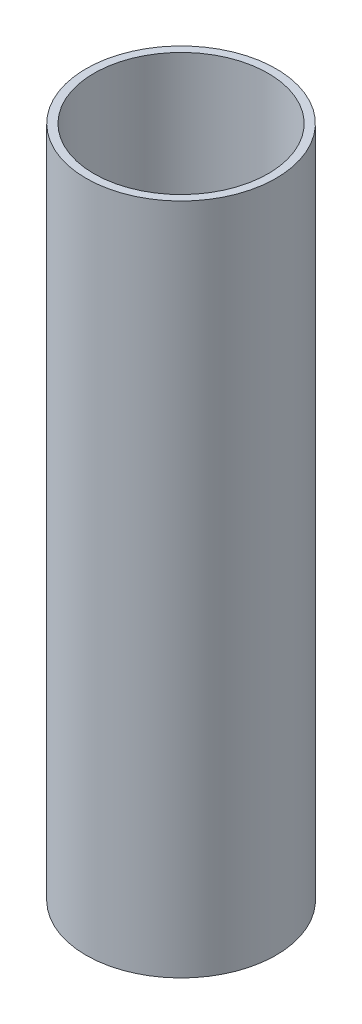
SolidWorks part; units mm, degrees
ref_plane "Front Plane" through (0, 0, 0) normal (0, 0, 1) x (1, 0, 0)
ref_plane "Top Plane" through (0, 0, 0) normal (0, 1, 0) x (1, 0, 0)
ref_plane "Right Plane" through (0, 0, 0) normal (1, 0, 0) x (0, 0, -1)
sketch "Sketch3" plane through (0, 0, 0) normal (0, 1, 0) x (1, 0, 0)
  circle A0 centre (0, 0) radius 12
  circle A1 centre (0, 0) radius 11
  dimension "D1" = 1
  dimension "D2" = 24
extrude "Boss-Extrude3" add sketch "Sketch3" along normal blind 85 contours A1
